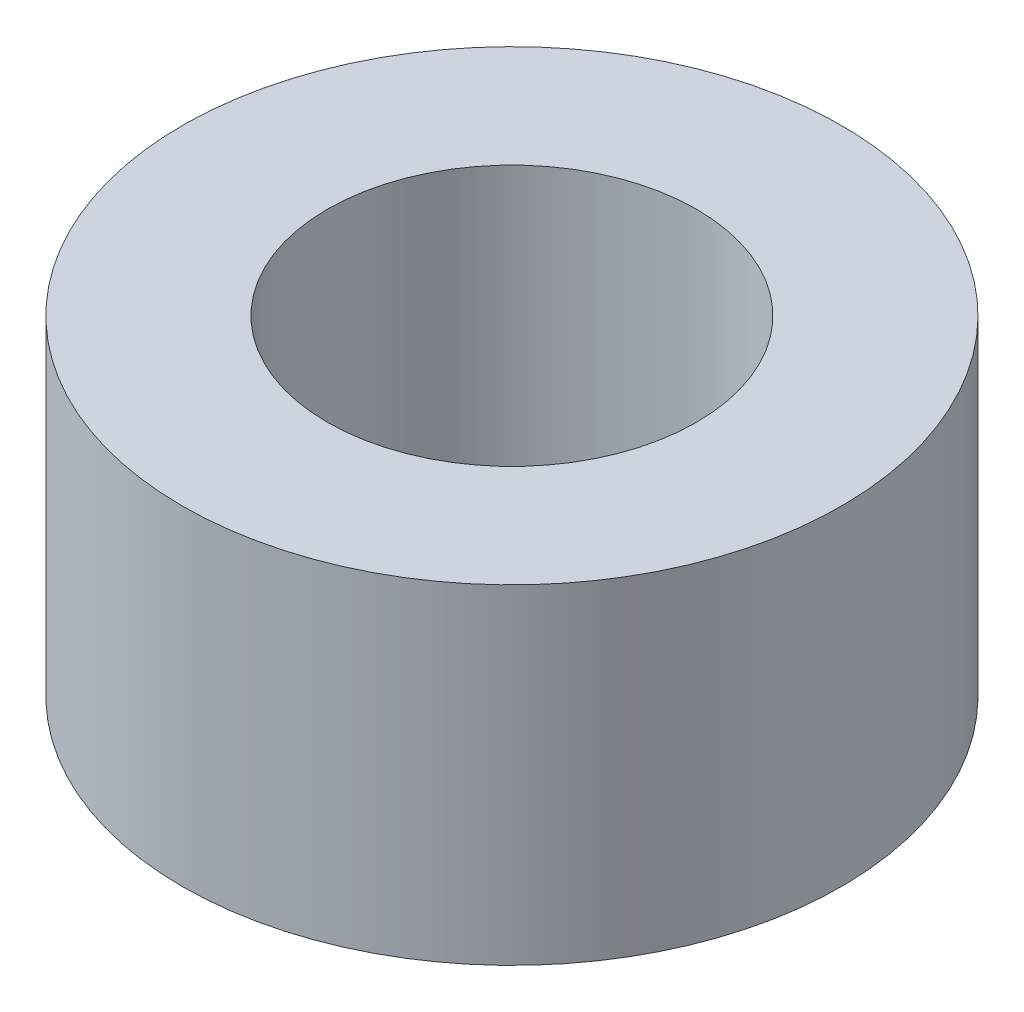
SolidWorks part; units mm, degrees
ref_plane "Front" through (0, 0, 0) normal (0, 0, 1) x (1, 0, 0)
ref_plane "Top" through (0, 0, 0) normal (0, 1, 0) x (1, 0, 0)
ref_plane "Right" through (0, 0, 0) normal (1, 0, 0) x (0, 0, -1)
sketch "Sketch1" plane through (0, 0, 0) normal (0, 1, 0) x (1, 0, 0)
  circle A0 centre (0, 0) radius 3.175
  dimension "D1" = 6.35
extrude "Boss-Extrude1" add sketch "Sketch1" along normal blind 3.175
sketch "Sketch2" plane through (0, 3.175, 0) normal (0, 1, 0) x (1, 0, 0)
  circle A0 centre (0, 0) radius 1.778
  dimension "D1" = 3.556
extrude "Cut-Extrude1" cut sketch "Sketch2" against normal through all
